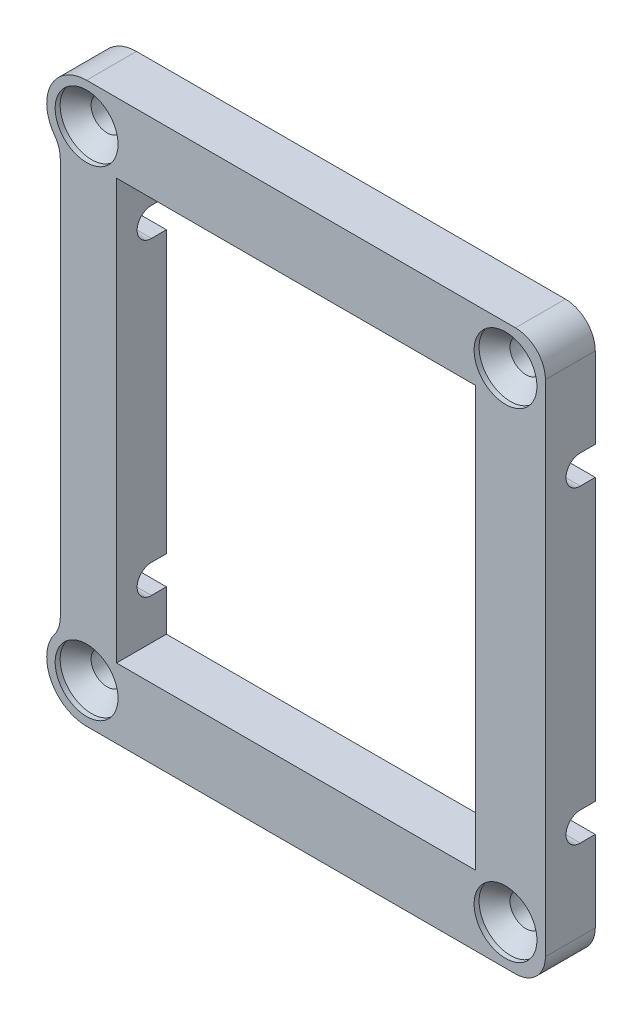
SolidWorks part; units mm, degrees
material "ABS"
ref_plane "Front Plane" through (0, 0, 0) normal (0, 0, 1) x (1, 0, 0)
ref_plane "Top Plane" through (0, 0, 0) normal (0, 1, 0) x (1, 0, 0)
ref_plane "Right Plane" through (0, 0, 0) normal (1, 0, 0) x (0, 0, -1)
sketch "Sketch1" plane through (0, 0, 0) normal (0, 0, 1) x (1, 0, 0)
  line L0 (23.0539, -73.6389) -> (23.0539, -115.7389)
  line L1 (20.0539, -66.6389) -> (63.0539, -66.6389)
  line L2 (17.4139, -73.644) -> (17.4139, -115.7339)
  line L3 (20.0539, -122.7389) -> (63.0539, -122.7389)
  line L4 (66.0539, -69.6389) -> (66.0539, -119.7389)
  line L10 (23.0539, -115.7389) -> (59.0539, -115.7389)
  line L12 (59.0539, -73.6389) -> (59.0539, -115.7389)
  line L13 (59.0539, -73.6389) -> (23.0539, -73.6389)
  line L15 (66.0539, -101.9889) -> (66.0539, -117.3889) construction
  line L17 (17.4139, -89.1889) -> (17.4139, -76.6389) construction
  arc A0 (63.0539, -66.6389) -> (66.0539, -69.6389) centre (63.0539, -69.6389) cw
  arc A3 (63.0539, -122.7389) -> (66.0539, -119.7389) centre (63.0539, -119.7389) ccw
  circle A4 centre (20.0539, -70.6389) radius 1.25
  circle A5 centre (20.0539, -118.7389) radius 1.25
  circle A6 centre (62.0539, -70.6389) radius 1.25
  circle A7 centre (62.0539, -118.7389) radius 1.25
  arc A8 (20.0539, -66.6389) -> (17.4139, -73.644) centre (20.0539, -70.6389) ccw
  arc A9 (17.4139, -115.7339) -> (20.0539, -122.7389) centre (20.0539, -118.7389) ccw
  dimension "D3" = 3
  dimension "D1" = 7
  dimension "D2" = 7
extrude "Boss-Extrude1" add sketch "Sketch1" along normal blind 5
hole_wizard "CSK for M3 Countersunk Flat Head Screw1" positions "Sketch3" profile "Sketch2" countersink size "M3" standard "ISO" end condition through all
sketch "Sketch3" plane through (0, 0, 5) normal (0, 0, 1) x (1, 0, 0)
  point P0 (20.0539, -118.7389)
  point P2 (20.0539, -70.6389)
  point P4 (62.0539, -70.6389)
  point P6 (62.0539, -118.7389)
sketch "Sketch2" plane through (20.0539, -118.7389, 5) normal (1, 0, 0) x (0, -1, 0)
  line L0 (0, 0) -> (0, 5)
  line L1 (0, 5) -> (1.6, 5)
  line L2 (1.6, 5) -> (1.6, 2.05)
  line L3 (1.6, 2.05) -> (3.15, 0.5)
  line L4 (3.15, 0.5) -> (3.15, 0)
  line L6 (3.15, 0) -> (0, 0)
  line L7 (-1.6, 2.05) -> (-3.15, 0.5) construction
  line L11 (0, -6.35) -> (0, 107.95) construction
  dimension "Thru Hole Dia." = 3.2
  dimension "Thru Hole Depth" = 5
  dimension "C'Sink Dia." = 6.3
  dimension "C'Sink Angle" = 90
  dimension "Head Clearance" = 0.5
hole_wizard "Furo com folga de M34" positions "Sketch5" profile "Sketch4" hole size "M3" standard "Ansi Metric" end condition through all
sketch "Sketch5" plane through (66.0539, 0, 0) normal (1, 0, 0) x (0, 0, -1)
  circle A1 centre (-1.5, -110.1889) radius 1.5
  circle A3 centre (-1.5, -79.1889) radius 1.5
  point P0 (-1.5, -79.1889)
  point P2 (-1.5, -110.1889)
sketch "Sketch4" plane through (66.0539, -79.1889, 1.5) normal (0, 1, 0) x (0, 0, -1)
  line L0 (0, 0) -> (0, 50)
  line L1 (0, 50) -> (1.435, 50)
  line L2 (1.435, 50) -> (1.435, 0)
  line L5 (1.435, 0) -> (0, 0)
  line L11 (0, -6.35) -> (0, 107.95) construction
  dimension "Thru Hole Dia." = 2.87
  dimension "Thru Hole Depth" = 50
fillet "Filete1" radius 3 2 edges at (17.4139, -115.7339, 2.5) (17.4139, -73.644, 2.5)
sketch "Esboço3" plane through (59.0539, 0, 0) normal (-1, 0, 0) x (0, 0, 1)
  line L1 (1.5, -80.6239) -> (0, -80.6239)
  line L2 (1.5, -80.6239) -> (1.5, -77.7539)
  line L3 (1.5, -77.7539) -> (0, -77.7539)
  line L4 (0, -80.6239) -> (0, -77.7539)
  line L5 (0, -73.6389) -> (0, -115.7389) construction
  line L6 (1.5, -108.7539) -> (0, -108.7539)
  line L7 (1.5, -108.7539) -> (1.5, -111.6239)
  line L8 (1.5, -111.6239) -> (0, -111.6239)
  line L9 (0, -108.7539) -> (0, -111.6239)
  circle A1 centre (1.5, -110.1889) radius 1.435 construction
  circle A2 centre (1.5, -110.1889) radius 1.435 construction
  circle A3 centre (1.5, -79.1889) radius 1.435 construction
extrude "Corte-extrusão1" cut sketch "Esboço3" along normal blind 63 and the other way blind 10
